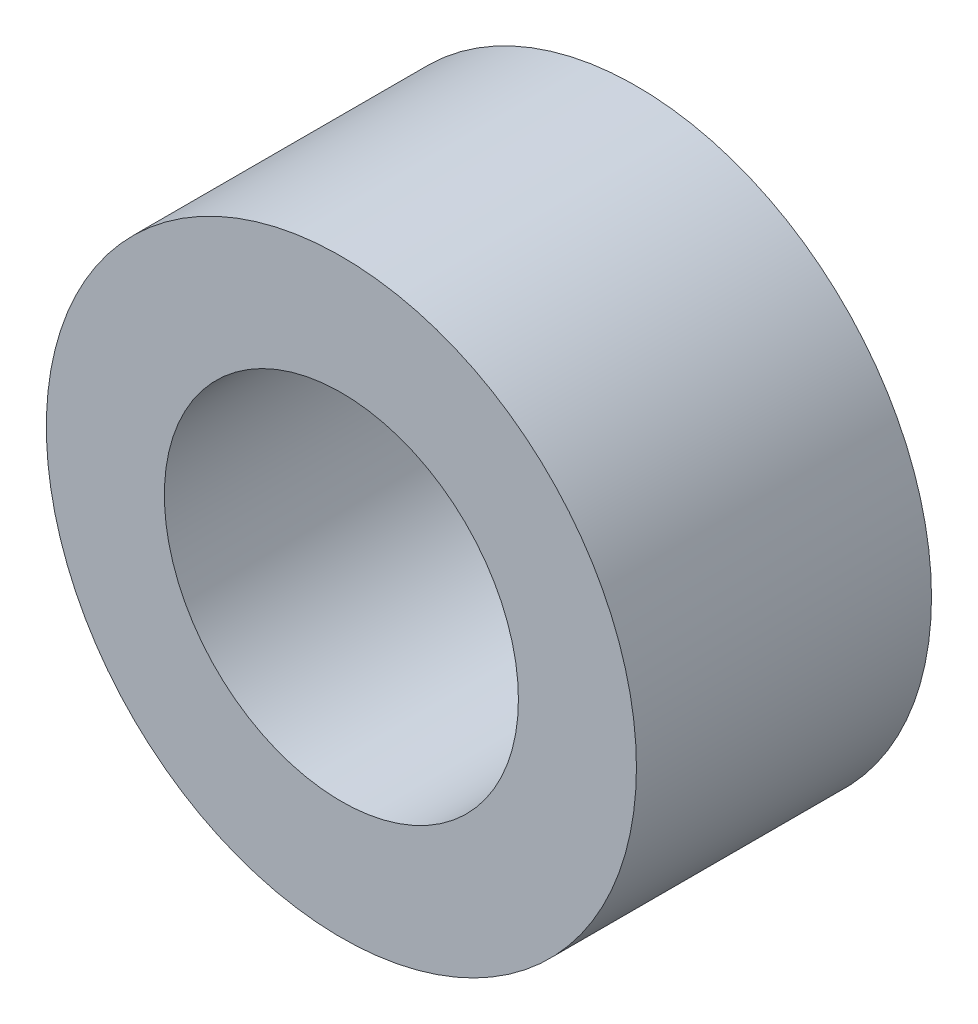
SolidWorks part; units mm, degrees
ref_plane "Front Plane" through (0, 0, 0) normal (0, 0, 1) x (1, 0, 0)
ref_plane "Top Plane" through (0, 0, 0) normal (0, 1, 0) x (1, 0, 0)
ref_plane "Right Plane" through (0, 0, 0) normal (1, 0, 0) x (0, 0, -1)
sketch "Sketch1" plane through (0, 0, 0) normal (0, 0, 1) x (1, 0, 0)
  circle A0 centre (0, 0) radius 10
  circle A1 centre (0, 0) radius 6
  dimension "D1" = 12
  dimension "D2" = 20
extrude "Boss-Extrude1" add sketch "Sketch1" along normal blind 10
equation "\"tubeOutDiameter\" = 35mm"
equation "\"wheelShaftDiameter\"= 12mm"
equation "\"wheelThickness\"= 135mm"
equation "\"BearingDiameter\"= 20mm"
equation "\"BearingThickness\"= 10mm"
equation "\"D1@Boss-Extrude1\"=\"BearingThickness\""
